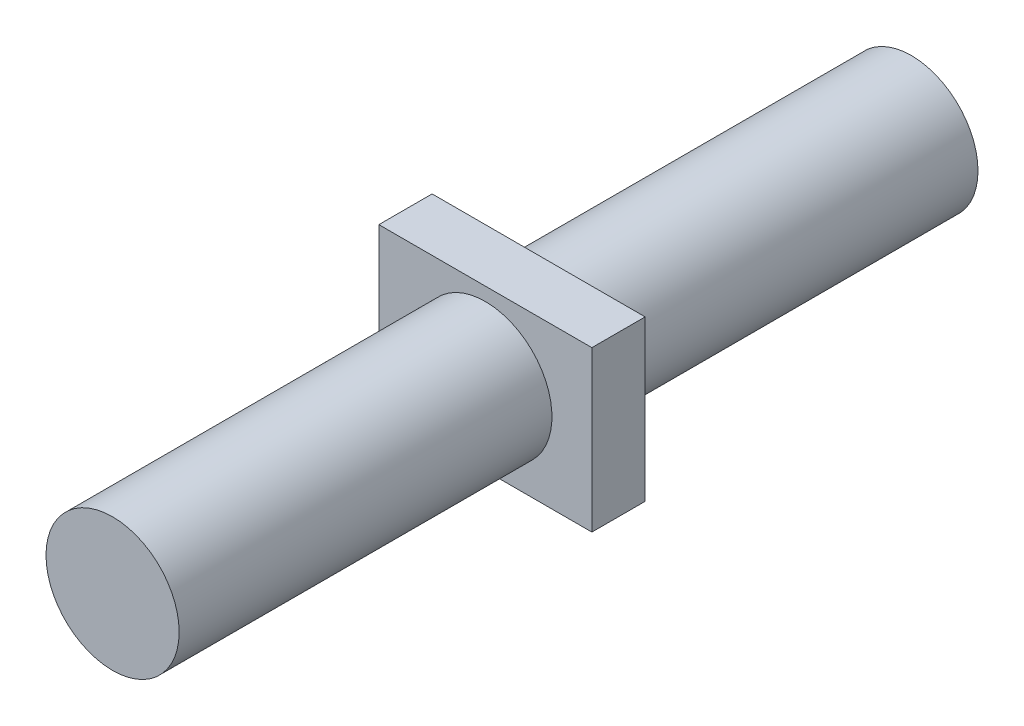
SolidWorks part; units mm, degrees
ref_plane "Front Plane" through (0, 0, 0) normal (0, 0, 1) x (1, 0, 0)
ref_plane "Top Plane" through (0, 0, 0) normal (0, 1, 0) x (1, 0, 0)
ref_plane "Right Plane" through (0, 0, 0) normal (1, 0, 0) x (0, 0, -1)
sketch "Sketch1" plane through (0, 0, 0) normal (0, 0, 1) x (1, 0, 0)
  circle A0 centre (0, 0) radius 12.5
  dimension "D1" = 25
extrude "Boss-Extrude1" add sketch "Sketch1" along normal blind 150
sketch "Sketch2" plane through (0, 0, 0) normal (0, 0, 1) x (1, 0, 0)
  line L1 (-20, -15) -> (20, -15)
  line L2 (-20, -15) -> (-20, 15)
  line L3 (-20, 15) -> (20, 15)
  line L4 (20, -15) -> (20, 15)
  line L5 (-20, -15) -> (20, 15) construction
  line L6 (-20, 15) -> (20, -15) construction
  point P0 (0, 0)
  dimension "D1" = 40
  dimension "D2" = 30
extrude "Boss-Extrude2" add sketch "Sketch2" along normal blind 5 and the other way blind 5 from offset 75
